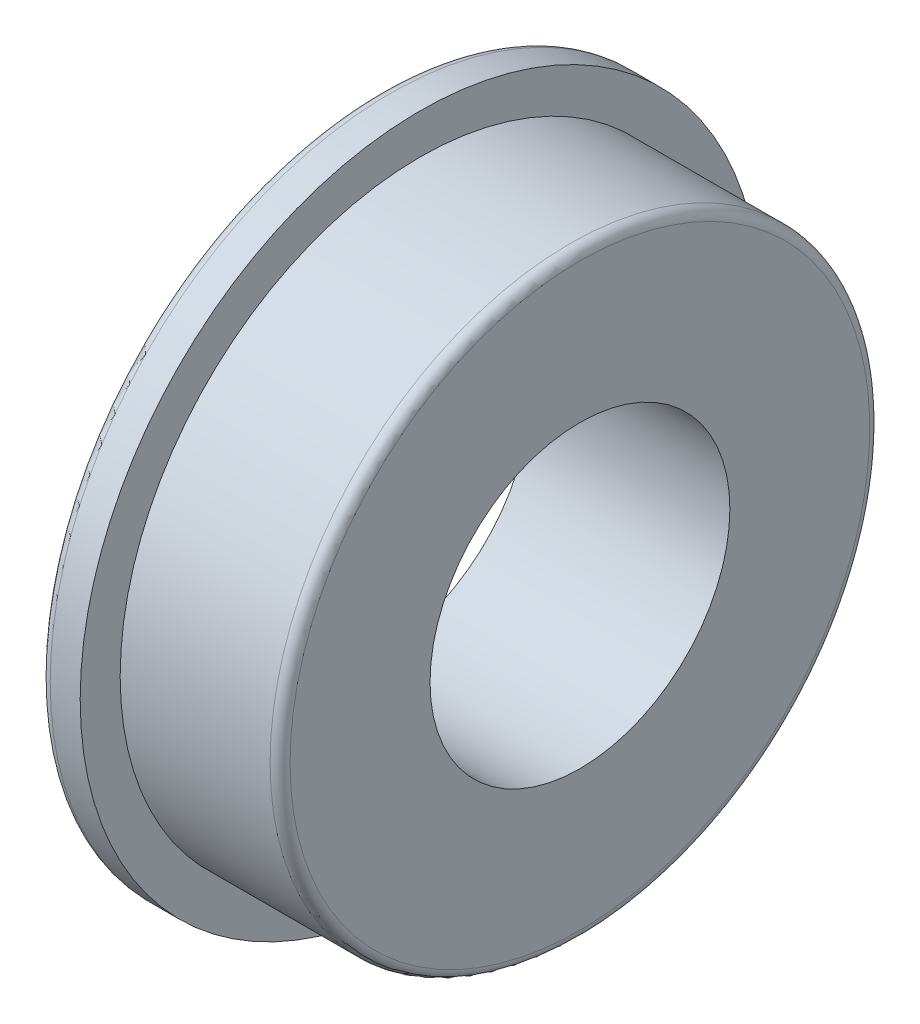
SolidWorks part; units mm, degrees
ref_plane "Front Plane" through (0, 0, 0) normal (0, 0, 1) x (1, 0, 0)
ref_plane "Top Plane" through (0, 0, 0) normal (0, 1, 0) x (1, 0, 0)
ref_plane "Right Plane" through (0, 0, 0) normal (1, 0, 0) x (0, 0, -1)
sketch "Sketch1" plane through (0, 0, 0) normal (0, 0, 1) x (1, 0, 0)
  line L0 (0, 0) -> (4, 0) construction
  line L1 (0, 3) -> (0, 6.8)
  line L2 (0, 6.8) -> (0.8, 6.8)
  line L3 (0.8, 6.8) -> (0.8, 6)
  line L4 (0.8, 6) -> (4, 6)
  line L5 (4, 6) -> (4, 3)
  line L6 (4, 3) -> (0, 3)
  dimension "D1" = 4
  dimension "D2" = 0.8
  dimension "D3" = 6
  dimension "D4" = 3
  dimension "D5" = 6.8
revolve "Revolve1" add sketch "Sketch1" angle 360 about L0
fillet "Fillet1" radius 0.2 2 edges at (0, 0, 6.8) (4, 0, 6)
